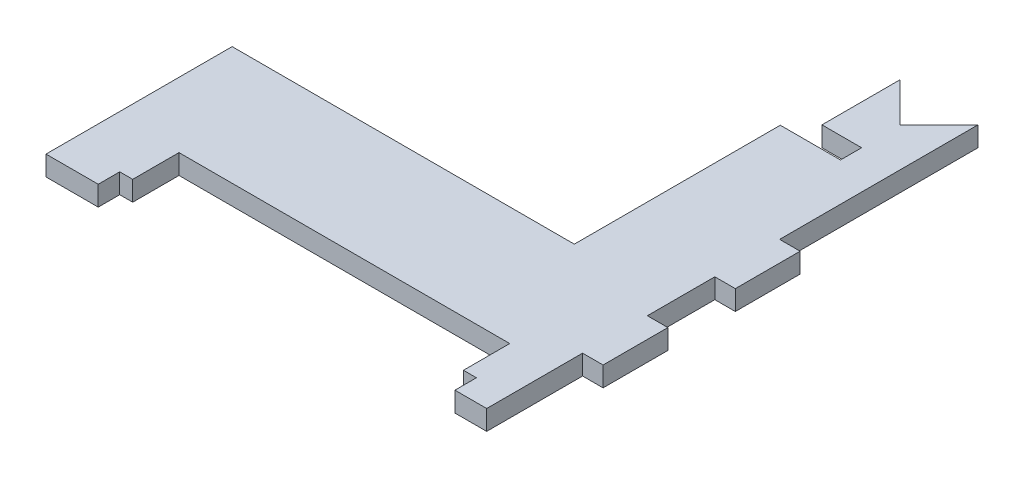
SolidWorks part; units mm, degrees
ref_plane "Front Plane" through (0, 0, 0) normal (0, 0, 1) x (1, 0, 0)
ref_plane "Top Plane" through (0, 0, 0) normal (0, 1, 0) x (1, 0, 0)
ref_plane "Right Plane" through (0, 0, 0) normal (1, 0, 0) x (0, 0, -1)
sketch "Sketch1" plane through (0, 0, 0) normal (0, 1, 0) x (1, 0, 0)
  line L0 (0, 0) -> (0, 75) construction
  line L1 (-34.8722, 0) -> (34.8722, 0)
  line L2 (-34.8722, 0) -> (-34.8722, 75) construction
  line L3 (-34.8722, 75) -> (34.8722, 75) construction
  line L4 (34.8722, 0) -> (34.8722, 75)
  line L5 (34.8722, 75) -> (34.8722, 0) construction
  line L6 (-34.8722, 75) -> (-34.8722, 0) construction
  line L7 (31.8722, 75) -> (25.8722, 69) construction
  line L8 (-34.8722, 75) -> (34.8722, 75) construction
  line L9 (34.8722, 75) -> (31.8722, 75)
  line L10 (16.8722, 75) -> (16.8722, 28.75)
  line L11 (16.8722, 28.75) -> (-34.8722, 28.75)
  line L12 (-34.8722, 28.75) -> (-34.8722, 0)
  line L13 (16.8722, 28.75) -> (-34.8722, 28.75) construction
  line L14 (16.8722, 75) -> (16.8722, 28.75) construction
  line L15 (-24.9087, 0) -> (-24.9087, 10.75) construction
  line L16 (-24.9087, 10.75) -> (24.9087, 10.75) construction
  line L17 (24.9087, 10.75) -> (24.9087, 0) construction
  line L18 (-24.9087, 10.75) -> (-24.9087, 3.75) construction
  line L19 (24.9087, 3.75) -> (24.9087, 10.75) construction
  line L20 (24.9087, 10.75) -> (-24.9087, 10.75) construction
  line L21 (-34.8722, 3.75) -> (34.8722, 3.75) construction
  line L22 (-34.8722, 3.75) -> (34.8722, 3.75) construction
  line L23 (-26.8722, 0) -> (-26.8722, 3.75) construction
  line L24 (26.8722, 0) -> (26.8722, 3.75) construction
  line L25 (25.8722, 69) -> (19.8722, 75) construction
  line L26 (31.8722, 75) -> (25.8722, 69)
  line L27 (25.8722, 69) -> (19.8722, 75)
  line L28 (19.8722, 75) -> (16.8722, 75)
  line L29 (31.8722, 75) -> (31.8722, 0) construction
  line L30 (31.8722, 75) -> (31.8722, 0) construction
  line L31 (31.8722, 65) -> (34.8722, 65) construction
  line L32 (34.8722, 55) -> (31.8722, 55) construction
  line L33 (31.8722, 45) -> (34.8722, 45) construction
  line L34 (34.8722, 35) -> (31.8722, 35) construction
  line L35 (34.8722, 25) -> (31.8722, 25) construction
  line L36 (34.8722, 5) -> (31.8722, 5) construction
  line L37 (34.8722, 15) -> (31.8722, 15) construction
  line L38 (31.8722, 65) -> (34.8722, 65) construction
  line L39 (34.8722, 55) -> (31.8722, 55) construction
  line L40 (31.8722, 45) -> (34.8722, 45) construction
  line L41 (34.8722, 35) -> (31.8722, 35) construction
  line L42 (34.8722, 25) -> (31.8722, 25) construction
  line L43 (34.8722, 5) -> (31.8722, 5) construction
  line L44 (34.8722, 15) -> (31.8722, 15) construction
  line L45 (25.8722, 63) -> (25.8722, 60) construction
  line L46 (16.8722, 63) -> (34.8722, 63) construction
  line L47 (34.8722, 60) -> (16.8722, 60) construction
  line L48 (16.8722, 63) -> (34.8722, 63) construction
  line L49 (34.8722, 60) -> (16.8722, 60) construction
  line L50 (19.8722, 75) -> (19.8722, 65) construction
  line L51 (19.8722, 65) -> (16.8722, 65) construction
  point P44 (-34.8722, 28.75)
sketch "Sketch2" plane through (0, 0, 0) normal (0, 0, 1) x (1, 0, 0)
  line L0 (-51.8722, 3) -> (51.8722, 3) construction
  line L1 (-34.8722, 0) -> (34.9722, 0)
  line L2 (-34.8722, 0) -> (-34.8722, 3)
  line L3 (-34.8722, 3) -> (34.9722, 3)
  line L4 (34.9722, 0) -> (34.9722, 3)
extrude "Boss-Extrude1" add sketch "Sketch1" along normal up to vertex (3 mm away) up to point (-34.8722, 3, 0)
sketch "Sketch3" plane through (0, 0, 0) normal (0, 1, 0) x (1, 0, 0)
  line L0 (-34.8722, 28.75) -> (-34.8722, 0) construction
  line L1 (-34.8722, 0) -> (34.8722, 0) construction
  line L2 (34.8722, 0) -> (34.8722, 75) construction
  line L3 (-34.8722, 0.5) -> (-34.8722, 0)
  line L4 (-34.8722, 0) -> (34.8722, 0)
  line L5 (34.8722, 0) -> (34.8722, 15)
  line L6 (24.9087, 10.75) -> (24.9087, 0) construction
  line L7 (-24.9087, 10.75) -> (24.9087, 10.75) construction
  line L8 (-24.9087, 0) -> (-24.9087, 10.75) construction
  line L9 (-34.8722, 3.75) -> (34.8722, 3.75) construction
  line L10 (-26.8722, 0) -> (-26.8722, 3.75) construction
  line L11 (26.8722, 0) -> (26.8722, 3.75) construction
  line L12 (24.9087, 10.75) -> (24.9087, 3.75)
  line L13 (-24.9087, 10.75) -> (24.9087, 10.75)
  line L14 (-24.9087, 3.75) -> (-24.9087, 10.75)
  line L15 (-26.8722, 3.75) -> (-24.9087, 3.75)
  line L16 (-26.8722, 0.5) -> (-26.8722, 3.75)
  line L17 (26.8722, 0.5) -> (26.8722, 3.75)
  line L18 (31.8722, 0.5) -> (26.8722, 0.5)
  line L19 (34.8722, 0.5) -> (-34.8722, 0.5) construction
  line L20 (24.9087, 3.75) -> (26.8722, 3.75)
  line L21 (-26.8722, 0.5) -> (-34.8722, 0.5)
  line L22 (31.8722, 25) -> (31.8722, 35)
  line L23 (34.8722, 55) -> (31.8722, 55) construction
  line L25 (19.8722, 75) -> (19.8722, 65) construction
  line L27 (34.8722, 45) -> (31.8722, 45)
  line L29 (34.8722, 35) -> (31.8722, 35)
  line L31 (34.8722, 25) -> (31.8722, 25)
  line L33 (34.8722, 15) -> (31.8722, 15)
  line L35 (16.8722, 63) -> (34.8722, 63) construction
  line L37 (34.8722, 75) -> (31.8722, 75)
  line L38 (34.8722, 75) -> (34.8722, 45)
  line L40 (19.8722, 63) -> (19.8722, 75)
  line L41 (19.8722, 75) -> (16.8722, 75)
  line L42 (16.8722, 60) -> (16.8722, 75)
  line L43 (19.8722, 63) -> (25.8722, 63)
  line L45 (16.8722, 60) -> (25.8722, 60)
  line L46 (25.8722, 63) -> (25.8722, 60)
  line L47 (31.8722, 75) -> (31.8722, 45)
  line L49 (34.8722, 35) -> (34.8722, 25)
  line L50 (31.8722, 75) -> (31.8722, 0) construction
  line L51 (31.8722, 15) -> (31.8722, 0.5)
  line L52 (31.8722, 60) -> (16.8722, 60) construction
  line L53 (34.8722, 60) -> (16.8722, 60) construction
  line L54 (25.8722, 63) -> (25.8722, 60) construction
sketch "Sketch6" plane through (0, 0, 0) normal (0, 1, 0) x (1, 0, 0)
  line L0 (31.7722, 75.1) -> (31.7722, 44.9)
  line L1 (31.7722, 44.9) -> (34.9722, 44.9)
  line L2 (34.9722, 44.9) -> (34.9722, 75.1)
  line L3 (34.9722, 75.1) -> (31.7722, 75.1)
  line L4 (31.8722, 75) -> (31.8722, 45)
  line L5 (31.8722, 45) -> (34.8722, 45)
  line L6 (34.8722, 45) -> (34.8722, 75)
  line L7 (34.8722, 75) -> (31.8722, 75)
  line L8 (31.8722, 75) -> (31.8722, 45) construction
  line L9 (31.8722, 45) -> (34.8722, 45) construction
  line L10 (34.8722, 45) -> (34.8722, 75) construction
  line L11 (34.8722, 75) -> (31.8722, 75) construction
  line L12 (31.8722, 35) -> (31.8722, 25)
  line L13 (34.8722, 35) -> (31.8722, 35)
  line L14 (34.8722, 25) -> (34.8722, 35)
  line L15 (31.8722, 25) -> (34.8722, 25)
  line L16 (31.8722, 35) -> (31.8722, 25) construction
  line L17 (34.8722, 35) -> (31.8722, 35) construction
  line L18 (34.8722, 25) -> (34.8722, 35) construction
  line L19 (31.8722, 25) -> (34.8722, 25) construction
  line L20 (31.7722, 35.1) -> (31.7722, 24.9)
  line L21 (31.7722, 24.9) -> (34.9722, 24.9)
  line L22 (25.8722, 63) -> (19.8722, 63)
  line L23 (19.8722, 63) -> (19.8722, 75)
  line L24 (19.8722, 75) -> (16.8722, 75)
  line L25 (16.8722, 75) -> (16.8722, 60)
  line L26 (16.8722, 60) -> (25.8722, 60)
  line L27 (25.8722, 60) -> (25.8722, 63)
  line L28 (25.8722, 63) -> (19.8722, 63) construction
  line L29 (19.8722, 63) -> (19.8722, 75) construction
  line L30 (34.8722, 0) -> (34.8722, 15)
  line L31 (-34.8722, 0) -> (34.8722, 0)
  line L32 (-34.8722, 0.5) -> (-34.8722, 0)
  line L33 (-26.8722, 0.5) -> (-34.8722, 0.5)
  line L34 (-26.8722, 3.75) -> (-26.8722, 0.5)
  line L35 (-24.9087, 3.75) -> (-26.8722, 3.75)
  line L36 (-24.9087, 10.75) -> (-24.9087, 3.75)
  line L37 (24.9087, 10.75) -> (-24.9087, 10.75)
  line L38 (24.9087, 3.75) -> (24.9087, 10.75)
  line L39 (26.8722, 3.75) -> (24.9087, 3.75)
  line L40 (26.8722, 0.5) -> (26.8722, 3.75)
  line L41 (31.8722, 0.5) -> (26.8722, 0.5)
  line L42 (31.8722, 15) -> (31.8722, 0.5)
  line L43 (34.8722, 15) -> (31.8722, 15)
  line L44 (34.8722, 0) -> (34.8722, 15) construction
  line L45 (-34.8722, 0) -> (34.8722, 0) construction
  line L46 (-34.8722, 0.5) -> (-34.8722, 0) construction
  line L47 (-26.8722, 0.5) -> (-34.8722, 0.5) construction
  line L48 (-26.8722, 3.75) -> (-26.8722, 0.5) construction
  line L49 (-24.9087, 3.75) -> (-26.8722, 3.75) construction
  line L50 (-24.9087, 10.75) -> (-24.9087, 3.75) construction
  line L51 (24.9087, 10.75) -> (-24.9087, 10.75) construction
  line L52 (24.9087, 3.75) -> (24.9087, 10.75) construction
  line L53 (26.8722, 3.75) -> (24.9087, 3.75) construction
  line L54 (26.8722, 0.5) -> (26.8722, 3.75) construction
  line L55 (31.8722, 0.5) -> (26.8722, 0.5) construction
  line L56 (31.8722, 15) -> (31.8722, 0.5) construction
  line L57 (34.8722, 15) -> (31.8722, 15) construction
  line L58 (19.8722, 75) -> (16.8722, 75) construction
  line L59 (16.8722, 75) -> (16.8722, 60) construction
  line L60 (16.8722, 60) -> (25.8722, 60) construction
  line L61 (25.8722, 60) -> (25.8722, 63) construction
  line L62 (34.9722, 24.9) -> (34.9722, 35.1)
  line L63 (34.9722, 35.1) -> (31.7722, 35.1)
  line L64 (25.9722, 63.1) -> (19.9722, 63.1)
  line L65 (19.9722, 63.1) -> (19.9722, 75.1)
  line L66 (19.9722, 75.1) -> (16.7722, 75.1)
  line L67 (16.7722, 75.1) -> (16.7722, 59.9)
  line L68 (16.7722, 59.9) -> (25.9722, 59.9)
  line L69 (25.9722, 59.9) -> (25.9722, 63.1)
  line L70 (34.9722, -0.1) -> (34.9722, 15.1)
  line L71 (34.9722, 15.1) -> (31.7722, 15.1)
  line L72 (31.7722, 15.1) -> (31.7722, 0.6)
  line L73 (31.7722, 0.6) -> (26.9722, 0.6)
  line L74 (26.9722, 0.6) -> (26.9722, 3.85)
  line L75 (26.9722, 3.85) -> (25.0087, 3.85)
  line L76 (25.0087, 3.85) -> (25.0087, 10.85)
  line L77 (25.0087, 10.85) -> (-25.0087, 10.85)
  line L78 (-25.0087, 10.85) -> (-25.0087, 3.85)
  line L79 (-25.0087, 3.85) -> (-26.9722, 3.85)
  line L80 (-26.9722, 3.85) -> (-26.9722, 0.6)
  line L81 (-26.9722, 0.6) -> (-34.9722, 0.6)
  line L82 (-34.9722, 0.6) -> (-34.9722, -0.1)
  line L83 (-34.9722, -0.1) -> (34.9722, -0.1)
  dimension "D1" = 0
  dimension "D2" = 0
  dimension "D3" = 0
  dimension "D4" = 0
  dimension "D5" = 0.1
extrude "Cut-Extrude3" cut sketch "Sketch6" along normal through all
